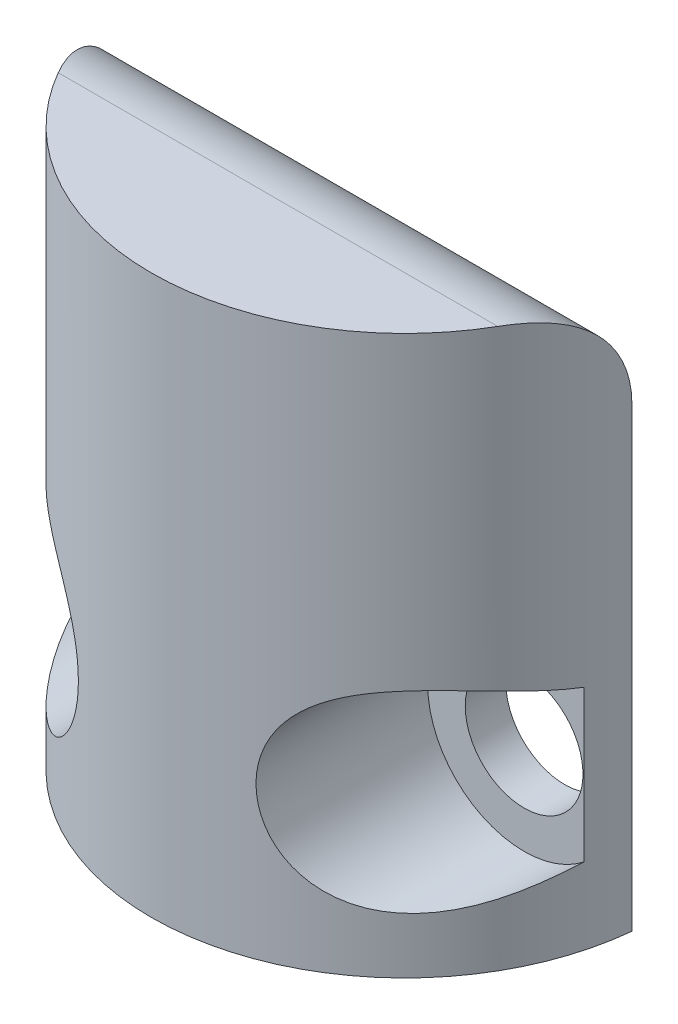
SolidWorks part; units mm, degrees
ref_plane "Front Plane" through (0, 0, 0) normal (0, 0, 1) x (1, 0, 0)
ref_plane "Top Plane" through (0, 0, 0) normal (0, 1, 0) x (1, 0, 0)
ref_plane "Right Plane" through (0, 0, 0) normal (1, 0, 0) x (0, 0, -1)
sketch "Sketch3" plane through (0, -12.7, 0) normal (0, -1, 0) x (1, 0, 0)
  line L0 (-6.35, 0.635) -> (6.35, 0.635)
  line L1 (-6.35, 0.635) -> (6.3182, 0.635)
  arc A0 (6.3182, 0.635) -> (-6.3182, 0.635) centre (0, 0) ccw
  arc A1 (6.3182, 0.635) -> (-6.3182, 0.635) centre (0, 0) ccw
extrude "Boss-Extrude1" add sketch "Sketch3" against normal blind 13.97 contours L1 A0
fillet "Fillet1" radius 2.54 1 edges at (0, 1.27, 0.635)
sketch "Sketch4" plane through (0, 0, 0.635) normal (0, 0, -1) x (-1, 0, 0)
  circle A0 centre (4.6355, -8.89) radius 1.4732
  circle A1 centre (-4.6355, -8.89) radius 1.4732
  dimension "D1" = 2.9464
extrude "Cut-Extrude1" cut sketch "Sketch4" against normal through all
ref_plane "Plane1" through (0, 0, 6.985) normal (0, 0, -1) x (-1, 0, 0)
sketch "Sketch6" plane through (0, 0, 6.985) normal (0, 0, -1) x (-1, 0, 0)
  circle A0 centre (4.6355, -8.89) radius 2.413
  circle A1 centre (-4.6355, -8.89) radius 2.413
extrude "Cut-Extrude3" cut sketch "Sketch6" along normal blind 5.334
